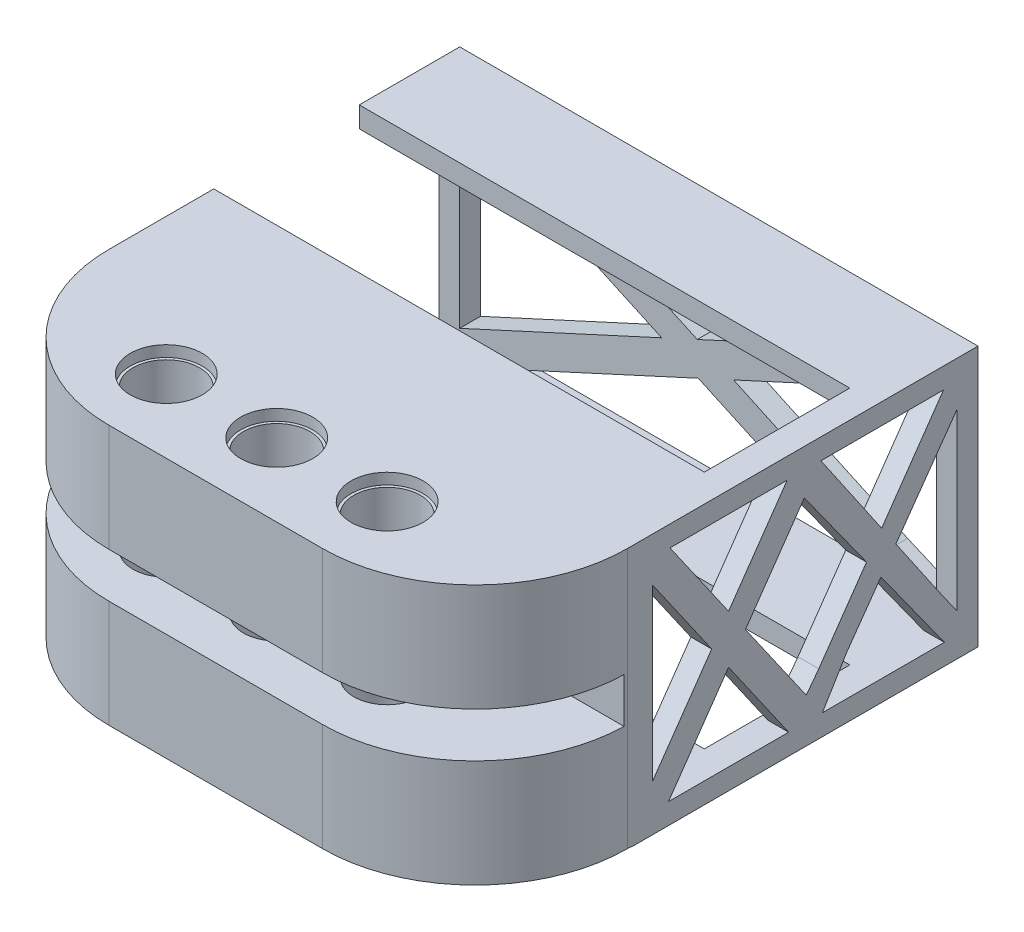
SolidWorks part; units mm, degrees
ref_plane "Front Plane" through (0, 0, 0) normal (0, 0, 1) x (1, 0, 0)
ref_plane "Top Plane" through (0, 0, 0) normal (0, 1, 0) x (1, 0, 0)
ref_plane "Right Plane" through (0, 0, 0) normal (1, 0, 0) x (0, 0, -1)
sketch "Sketch1" plane through (0, 0, 0) normal (0, 0, 1) x (1, 0, 0)
  line L1 (0, 0) -> (37.4, 0)
  line L2 (0, 0) -> (0, 18.8)
  line L3 (0, 18.8) -> (37.4, 18.8)
  line L4 (37.4, 0) -> (37.4, 18.8)
  dimension "D1" = 18.8
  dimension "D2" = 37.4
extrude "Boss-Extrude1" add sketch "Sketch1" along normal blind 2
sketch "Sketch2" plane through (0, 0, 2) normal (0, 0, 1) x (1, 0, 0)
  line L0 (37.4, 0) -> (37.4, 18.8) construction
  line L1 (0, 18.8) -> (37.4, 18.8)
  line L2 (0, 18.8) -> (0, 16.8)
  line L3 (2, 17.3) -> (35.4, 17.3)
  line L4 (37.4, 18.8) -> (37.4, 17.3)
  line L5 (2, 0) -> (0, 0)
  line L6 (0, 0) -> (37.4, 0)
  line L7 (0, 0) -> (0, 2)
  line L8 (2, 1.5) -> (35.4, 1.5)
  line L9 (37.4, 0) -> (37.4, 1.5)
  line L10 (0, 0) -> (2, 0)
  line L11 (0, 0) -> (0, 16.8)
  line L13 (2, 1.5) -> (2, 17.3)
  line L14 (37.4, 0) -> (35.9, 0)
  line L15 (37.4, 0) -> (35.9, 0)
  line L16 (37.4, 0) -> (37.4, 17.3)
  line L18 (35.4, 1.5) -> (35.4, 17.3)
  line L19 (37.4, 0) -> (35.9, 0)
  line L21 (37.4, 10.0292) -> (35.4, 10.0292) construction
  dimension "D1" = 2
  dimension "D2" = 2
  dimension "D3" = 2
  dimension "D4" = 2
  dimension "D5" = 33.4
  dimension "D6" = 15.8
extrude "Boss-Extrude2" add sketch "Sketch2" along normal blind 23
sketch "Sketch3" plane through (0, 0, 0) normal (0, -1, 0) x (1, 0, 0)
  line L2 (18.7, 0) -> (18.7, 1.5) construction
  line L4 (0, 0) -> (37.4, 0) construction
  line L9 (1.5, 23.5) -> (35.9, 23.5)
  line L10 (1.5, 23.5) -> (1.5, 1.5)
  line L11 (1.5, 1.5) -> (35.9, 1.5)
  line L12 (35.9, 23.5) -> (35.9, 1.5)
  dimension "D1" = 34.4
  dimension "D2" = 22
  dimension "D3" = 1.5
sketch "Sketch4" plane through (0, 0, 0) normal (-1, 0, 0) x (0, 0, 1)
  line L0 (1.5, 9.4) -> (0, 9.4) construction
  line L4 (23.5, 0) -> (23.5, 1.5) construction
  line L5 (25, 0) -> (0, 0) construction
  line L8 (23.5, 1.5) -> (25, 1.5) construction
  line L9 (1.5, 17.3) -> (23.5, 17.3)
  line L10 (1.5, 17.3) -> (1.5, 1.5)
  line L11 (1.5, 1.5) -> (23.5, 1.5)
  line L12 (23.5, 17.3) -> (23.5, 1.5)
  dimension "D1" = 15.8
  dimension "D2" = 22
  dimension "D3" = 1.5
  dimension "D4" = 1.5
  dimension "D5" = 1.5
extrude "Cut-Extrude3" cut sketch "Sketch4" against normal blind 5550
sketch "Sketch6" plane through (0, 0, 0) normal (0, 0, -1) x (-1, 0, 0)
  line L0 (-35.9, 18.8) -> (-35.9, 17.3) construction
  line L1 (-37.4, 18.8) -> (0, 18.8) construction
  line L2 (-35.9, 17.3) -> (-37.4, 17.3) construction
  line L3 (-37.4, 0) -> (-37.4, 18.8) construction
  line L4 (-1.5, 0) -> (-1.5, 1.5) construction
  line L5 (0, 0) -> (-37.4, 0) construction
  line L6 (-1.5, 1.5) -> (0, 1.5) construction
  line L7 (0, 18.8) -> (0, 0) construction
  line L9 (-35.9, 17.3) -> (-1.5, 17.3)
  line L10 (-35.9, 17.3) -> (-35.9, 1.5)
  line L11 (-35.9, 1.5) -> (-1.5, 1.5)
  line L12 (-1.5, 17.3) -> (-1.5, 1.5)
  dimension "D1" = 1.5
  dimension "D2" = 1.5
  dimension "D3" = 1.5
  dimension "D4" = 1.5
extrude "Cut-Extrude4" cut sketch "Sketch6" against normal blind 5550
sketch "Sketch7" plane through (0, 18.8, 0) normal (0, 1, 0) x (1, 0, 0)
  line L0 (1.635, 0) -> (1.635, -2) construction
  line L1 (37.4, 0) -> (0, 0) construction
  line L2 (1.635, -25) -> (1.635, -23) construction
  line L3 (37.4, -25) -> (0, -25) construction
  line L4 (37.4, -12.5) -> (35.4, -12.5) construction
  line L5 (37.4, -25) -> (37.4, 0) construction
  line L6 (0, -25) -> (0, 0) construction
  line L7 (1.635, -2) -> (35.4, -2)
  line L9 (1.635, -23) -> (35.4, -23)
  line L10 (35.4, -2) -> (35.4, -23)
  line L11 (1.635, -2) -> (0, -2)
  line L13 (1.635, -23) -> (0, -23)
  line L14 (0, -2) -> (0, -23)
  dimension "D1" = 2
  dimension "D2" = 2
  dimension "D3" = 2
extrude "Cut-Extrude5" cut sketch "Sketch7" against normal blind 5550
sketch "Sketch8" plane through (0, 0, 0) normal (0, 0, -1) x (-1, 0, 0)
  line L0 (-35.9, 16.089) -> (-35.9, 17.3)
  line L1 (-35.9, 17.3) -> (-33.2635, 17.3)
  line L2 (-1.5, 1.5) -> (-1.5, 17.3) construction
  line L3 (-33.2635, 1.5) -> (-35.9, 1.5)
  line L4 (-35.9, 1.5) -> (-35.9, 2.711)
  line L5 (-5.9578, 2.3365) -> (-18.7126, 8.1948)
  line L6 (-35.9, 17.3) -> (-35.9, 1.5) construction
  line L7 (-5.0392, 4.3365) -> (-16.0742, 9.4049)
  line L8 (-1.5, 17.3) -> (-35.9, 17.3) construction
  line L9 (-5.9578, 2.3365) -> (-4.1365, 1.5)
  line L10 (-35.9, 1.5) -> (-1.5, 1.5) construction
  line L11 (-5.0392, 4.3365) -> (-1.5, 2.711)
  line L12 (-31.9015, 3.3365) -> (-32.3189, 4.2453) construction
  line L13 (-31.9015, 3.3365) -> (-31.4861, 2.3365) construction
  line L14 (-32.3189, 4.2453) -> (-21.2634, 9.3664)
  line L15 (-31.4861, 2.3365) -> (-18.7126, 8.1948)
  line L16 (-31.4861, 2.3365) -> (-33.2635, 1.5)
  line L17 (-32.3189, 4.2453) -> (-35.9, 2.711)
  line L18 (-21.2634, 9.3664) -> (-35.9, 16.089)
  line L19 (-4.1365, 1.5) -> (-1.5, 1.5)
  line L20 (-18.6381, 10.5825) -> (-33.2635, 17.3)
  line L21 (-1.5, 1.5) -> (-1.5, 2.711)
  line L22 (-16.0742, 9.4049) -> (-1.5, 16.089)
  line L23 (-18.6381, 10.5825) -> (-4.1365, 17.3)
  line L24 (-1.5, 16.089) -> (-1.5, 17.3)
  line L25 (-1.5, 17.3) -> (-4.1365, 17.3)
  dimension "D3" = 1
  dimension "D4" = 1
  dimension "D5" = 29.9861
  dimension "D6" = 28.1824
  dimension "D7" = 3.896
extrude "Boss-Extrude3" add sketch "Sketch8" against normal blind 1.5
sketch "Sketch9" plane through (0, 0, 25) normal (0, 0, 1) x (1, 0, 0)
  line L0 (21.3365, 9.4) -> (35.9, 16.089)
  line L1 (18.7, 8.189) -> (33.2635, 1.5)
  line L2 (30.9269, 3.7842) -> (35.9, 1.5) construction
  line L4 (1.5, 2.711) -> (1.5, 1.5)
  line L6 (30.9269, 3.7842) -> (31.3487, 4.6947) construction
  line L7 (21.2634, 9.3664) -> (32.3189, 4.2453) construction
  line L8 (30.9269, 3.7842) -> (30.4756, 2.8) construction
  line L9 (31.4861, 2.3365) -> (18.7126, 8.1948) construction
  line L10 (4.1365, 1.5) -> (18.7, 8.189)
  line L11 (1.5, 2.711) -> (16.0635, 9.4)
  line L12 (1.5, 16.089) -> (16.0635, 9.4)
  line L13 (4.1365, 17.3) -> (18.7, 10.611)
  line L14 (1.5, 16.089) -> (1.5, 17.3)
  line L15 (18.7, 10.611) -> (33.2635, 17.3)
  line L16 (21.3365, 9.4) -> (35.9, 2.711)
  line L17 (1.5, 1.5) -> (4.1365, 1.5)
  line L18 (33.2635, 1.5) -> (35.9, 1.5)
  line L19 (1.5, 17.3) -> (4.1365, 17.3)
  line L20 (33.2635, 17.3) -> (35.9, 17.3)
  line L21 (35.9, 1.5) -> (35.9, 2.711)
  line L23 (35.9, 17.3) -> (35.9, 16.089)
extrude "Boss-Extrude4" add sketch "Sketch9" against normal blind 1.5
sketch "Sketch10" plane through (37.4, 0, 0) normal (1, 0, 0) x (0, 0, -1)
  line L0 (-23.5, 15.6274) -> (-23.5, 17.3)
  line L1 (-1.5, 1.5) -> (-23.5, 1.5) construction
  line L2 (-23.5, 17.3) -> (-22.2275, 17.3)
  line L3 (-23.5, 17.3) -> (-1.5, 17.3) construction
  line L4 (-23.5, 3.3278) -> (-23.5, 1.5)
  line L5 (-1.5, 17.3) -> (-1.5, 1.5) construction
  line L6 (-23.5, 1.5) -> (-22.3356, 1.5)
  line L7 (-18, 11.2278) -> (-13.7725, 17.3)
  line L8 (-16.7815, 9.4776) -> (-12.5352, 15.5768)
  line L9 (-13.6644, 1.5) -> (-11.2275, 1.5)
  line L10 (-12.3955, 3.1778) -> (-12.446, 1.5)
  line L11 (-22.7714, 4.3744) -> (-23.5, 3.3278)
  line L12 (-23.5, 1.5) -> (-23.5, 17.3) construction
  line L13 (-21.13, 3.2316) -> (-18, 7.7274)
  line L14 (-21.13, 3.2316) -> (-22.3356, 1.5)
  line L15 (-22.7714, 4.3744) -> (-19.2185, 9.4776)
  line L16 (-14.87, 3.2316) -> (-18, 7.7274)
  line L17 (-14.87, 3.2316) -> (-13.6644, 1.5)
  line L18 (-13.2286, 4.3744) -> (-12.3955, 3.1778)
  line L19 (-13.2286, 4.3744) -> (-16.7815, 9.4776)
  line L20 (-10.4989, 4.3744) -> (-11.4905, 4.3744) construction
  line L21 (-11.4905, 4.3744) -> (-9.4905, 4.3744) construction
  line L22 (-2.4276, 1.5) -> (-1.5, 1.5)
  line L23 (-1.5, 1.5) -> (-1.5, 2.9935)
  line L24 (-4.4915, 4.3744) -> (-7.0049, 7.8748)
  line L25 (-2.4915, 4.3744) -> (-5.9261, 9.3941)
  line L26 (-4.4915, 4.3744) -> (-2.4276, 1.5)
  line L27 (-2.4915, 4.3744) -> (-1.5, 2.9935)
  line L28 (-11.4905, 4.3744) -> (-12.3955, 3.1778)
  line L29 (-9.4905, 4.3744) -> (-11.2275, 1.5)
  line L30 (-11.4905, 4.3744) -> (-8.045, 9.3233)
  line L31 (-9.4905, 4.3744) -> (-7.0049, 7.8748)
  line L32 (-19.2185, 9.4776) -> (-23.5, 15.6274)
  line L33 (-8.045, 9.3233) -> (-12.5352, 15.5768)
  line L34 (-6.9519, 10.8933) -> (-2.4915, 17.3)
  line L35 (-1.5, 15.6274) -> (-1.5, 17.3)
  line L36 (-6.9519, 10.8933) -> (-11.3356, 17.3)
  line L37 (-5.9261, 9.3941) -> (-1.5, 15.6274)
  line L38 (-18, 11.2278) -> (-22.2275, 17.3)
  line L39 (-11.3356, 17.3) -> (-13.7725, 17.3)
  line L40 (-1.5, 17.3) -> (-2.4915, 17.3)
  line L41 (-22.2275, 17.3) -> (-23.5, 17.3)
  dimension "D1" = 2
  dimension "D2" = 2
  dimension "D3" = 2
extrude "Boss-Extrude5" add sketch "Sketch10" against normal blind 1.5
sketch "Sketch11" plane through (0, 18.8, 0) normal (0, 1, 0) x (1, 0, 0)
  line L0 (0, 0) -> (0, -7.25) construction
  line L1 (0, -23) -> (0, -15.75) construction
  line L3 (0, -7.25) -> (35.4, -7.25)
  line L4 (0, -7.25) -> (0, -2)
  line L5 (0, -2) -> (35.4, -2)
  line L6 (35.4, -7.25) -> (35.4, -2)
  dimension "D1" = 7.25
  dimension "D2" = 7.25
extrude "Boss-Extrude6" add sketch "Sketch11" against normal blind 1.5
sketch "Sketch12" plane through (0, 18.8, 0) normal (0, 1, 0) x (1, 0, 0)
  line L0 (0, -25) -> (0, -17.75) construction
  line L1 (35.4, -23) -> (35.4, -7.25) construction
  line L2 (0, -25) -> (35.4, -25)
  line L3 (0, -25) -> (0, -17.75)
  line L4 (0, -17.75) -> (35.4, -17.75)
  line L5 (35.4, -25) -> (35.4, -17.75)
  dimension "D1" = 7.25
extrude "Boss-Extrude7" add sketch "Sketch12" against normal blind 1.5
sketch "Sketch13" plane through (0, 0, 0) normal (0, -1, 0) x (1, 0, 0)
  line L1 (0, 17.75) -> (35.4, 17.75)
  line L2 (0, 17.75) -> (0, 23)
  line L3 (0, 23) -> (35.4, 23)
  line L4 (35.4, 17.75) -> (35.4, 23)
extrude "Boss-Extrude8" add sketch "Sketch13" against normal blind 1.5
sketch "Sketch14" plane through (0, 0, 0) normal (0, -1, 0) x (1, 0, 0)
  line L1 (0, 2) -> (35.4, 2)
  line L2 (0, 2) -> (0, 7.25)
  line L3 (0, 7.25) -> (35.4, 7.25)
  line L4 (35.4, 2) -> (35.4, 7.25)
extrude "Boss-Extrude9" add sketch "Sketch14" against normal blind 1.5
sketch "Sketch15" plane through (0, 18.8, 0) normal (0, 1, 0) x (1, 0, 0)
  line L0 (37.4, -12.5) -> (37.4, 2.35) construction
  line L1 (37.4, -25) -> (37.4, 0) construction
  line L3 (37.4, 2.35) -> (0, 2.35)
  line L4 (37.4, 2.35) -> (37.4, 0)
  line L5 (37.4, 0) -> (0, 0)
  line L6 (0, 2.35) -> (0, 0)
  dimension "D1" = 14.85
extrude "Boss-Extrude10" add sketch "Sketch15" against normal blind 1.5
sketch "Sketch16" plane through (0, 18.8, 0) normal (0, 1, 0) x (1, 0, 0)
  line L1 (37.4, 2.35) -> (0, 2.35)
  line L2 (37.4, 2.35) -> (37.4, 0)
  line L3 (37.4, 0) -> (0, 0)
  line L4 (0, 2.35) -> (0, 0)
extrude "Cut-Extrude6" cut sketch "Sketch16" against normal blind 10
sketch "Sketch17" plane through (0, 18.8, 0) normal (0, 1, 0) x (1, 0, 0)
  line L0 (37.4, -12.5) -> (25.8, -12.5) construction
  line L1 (37.4, -25) -> (37.4, 0) construction
  line L2 (25.8, -12.5) -> (25.8, -31.04) construction
  line L3 (25.8, -31.04) -> (17.83, -31.04) construction
  line L4 (0, -25) -> (37.4, -25)
  line L5 (0, -25) -> (0, -36.3)
  line L6 (0, -36.3) -> (37.4, -36.3)
  line L7 (37.4, -25) -> (37.4, -36.3)
  line L8 (17.83, -31.04) -> (9.86, -31.04) construction
  circle A0 centre (25.8, -31.04) radius 2.4
  circle A1 centre (17.83, -31.04) radius 2.4
  circle A2 centre (9.86, -31.04) radius 2.4
  dimension "D3" = 4.8
  dimension "D5" = 4.8
  dimension "D7" = 4.8
  dimension "D1" = 11.6
  dimension "D2" = 18.54
  dimension "D4" = 7.97
  dimension "D6" = 7.97
  dimension "D8" = 11.3
  dimension "D9" = 37.4
extrude "Boss-Extrude11" add sketch "Sketch17" against normal blind 18.76
fillet "Fillet2" radius 11 1 edges at (0, 9.42, 36.3)
fillet "Fillet3" radius 11 1 edges at (37.4, 9.42, 36.3)
sketch "Sketch21" plane through (0, 0, 36.3) normal (0, 0, 1) x (1, 0, 0)
  line L0 (11, 18.8) -> (26.4, 18.8) construction
  line L1 (-2.5432, 11.04) -> (39.1424, 11.04)
  line L2 (-2.5432, 11.04) -> (-2.5432, 7.8)
  line L3 (-2.5432, 7.8) -> (39.1424, 7.8)
  line L4 (39.1424, 11.04) -> (39.1424, 7.8)
  dimension "D1" = 3.24
  dimension "D2" = 7.76
extrude "Cut-Extrude7" cut sketch "Sketch21" against normal blind 10.76
sketch "Sketch22" plane through (0, 0.04, 0) normal (0, -1, 0) x (1, 0, 0)
  circle A1 centre (9.86, 31.04) radius 2.6
  circle A2 centre (17.83, 31.04) radius 2.6
  circle A3 centre (25.8, 31.04) radius 2.6
  dimension "D1" = 5.2
  dimension "D2" = 5.2
  dimension "D3" = 5.2
extrude "Cut-Extrude8" cut sketch "Sketch22" against normal blind 0.8
sketch "Sketch23" plane through (0, 18.8, 0) normal (0, 1, 0) x (1, 0, 0)
  circle A0 centre (9.86, -31.04) radius 2.6
  circle A1 centre (17.83, -31.04) radius 2.6
  circle A2 centre (25.8, -31.04) radius 2.6
  dimension "D1" = 5.2
  dimension "D2" = 5.2
  dimension "D3" = 5.2
extrude "Cut-Extrude9" cut sketch "Sketch23" against normal blind 0.8
